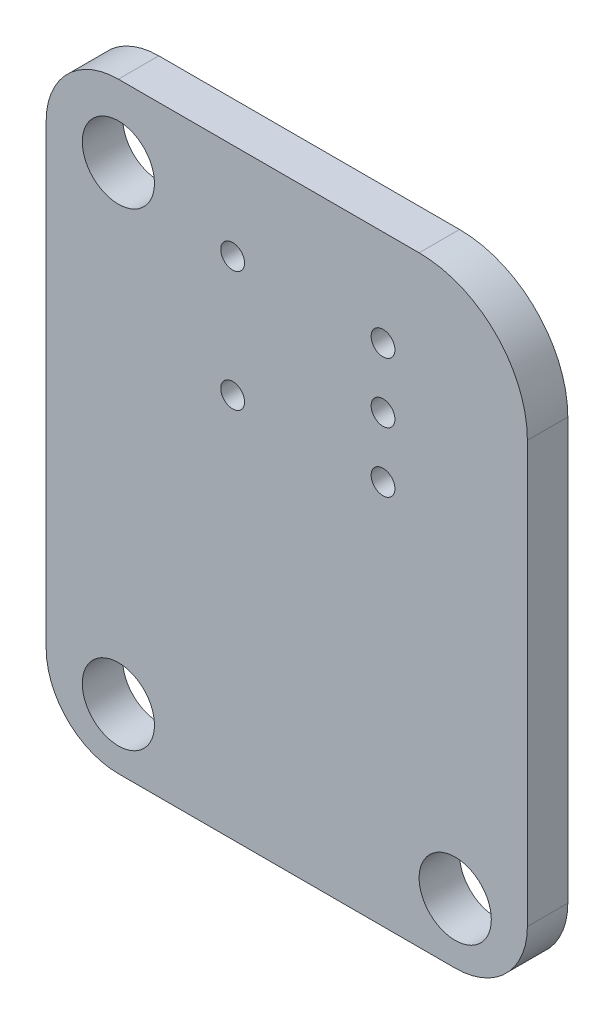
SolidWorks part; units mm, degrees
ref_plane "Front Plane" through (0, 0, 0) normal (0, 0, 1) x (1, 0, 0)
ref_plane "Top Plane" through (0, 0, 0) normal (0, 1, 0) x (1, 0, 0)
ref_plane "Right Plane" through (0, 0, 0) normal (1, 0, 0) x (0, 0, -1)
sketch "Sketch1" plane through (0, 0, -4.7) normal (0, 0, 1) x (1, 0, 0)
  line L0 (82.5, 65) -> (4.5, 65) construction
  line L1 (100, 26.864) -> (100, 37.5) construction
  line L2 (100, 43) -> (100, 60.5)
  line L3 (95.5, 65) -> (83, 65)
  line L4 (97, 40) -> (83, 40)
  line L5 (80, 43) -> (80, 62)
  arc A0 (100.5, 60.5) -> (95.5, 65.5) centre (95.5, 60.5) ccw construction
  arc A3 (100, 60.5) -> (95.5, 65) centre (95.5, 60.5) ccw
  arc A4 (83, 65) -> (80, 62) centre (83, 62) ccw
  arc A6 (83, 40) -> (80, 43) centre (83, 43) cw
  arc A7 (97, 40) -> (100, 43) centre (97, 43) ccw
  arc A18 (83, 59) -> (85.9468, 61.4375) centre (83, 62) ccw construction
  arc A19 (83, 59) -> (85.9468, 61.4375) centre (83, 62) ccw construction
  dimension "D1" = 25
extrude "BOARD" add sketch "Sketch1" along normal blind 1.68 separate body
sketch "Sketch2" plane through (0, 0, 0) normal (0, 0, 1) x (1, 0, 0)
  circle A0 centre (83, 42.5) radius 1.5
  circle A1 centre (97, 42.5) radius 1.5
  circle A2 centre (97, 35.5) radius 1.5
  circle A6 centre (83, 62) radius 1.5
  circle A7 centre (87.75, 56) radius 0.4953
  circle A8 centre (87.75, 61) radius 0.4953
  circle A9 centre (94, 58.5) radius 0.4953
  circle A10 centre (94, 56) radius 0.4953
  circle A11 centre (94, 61) radius 0.4953
  dimension "D1" = 3
extrude "PLATED HOLES" cut sketch "Sketch2" against normal through all
ref_plane "Plane1" through (0, 0, 0.8992) normal (0, 0, 1) x (1, 0, 0)
sketch "Sketch3" plane through (0, 0, 0) normal (0, 0, 1) x (1, 0, 0)
  line L0 (85.6, 63.45) -> (100.1, 63.45)
  line L1 (100.1, 63.45) -> (100.1, 53.55)
  line L2 (100.1, 53.55) -> (85.6, 53.55)
  line L3 (85.6, 53.55) -> (85.6, 63.45)
extrude "ENCODER_PEC09-2320F-S0015-1" [suppressed] add sketch "Sketch3" against normal blind 0.0254
